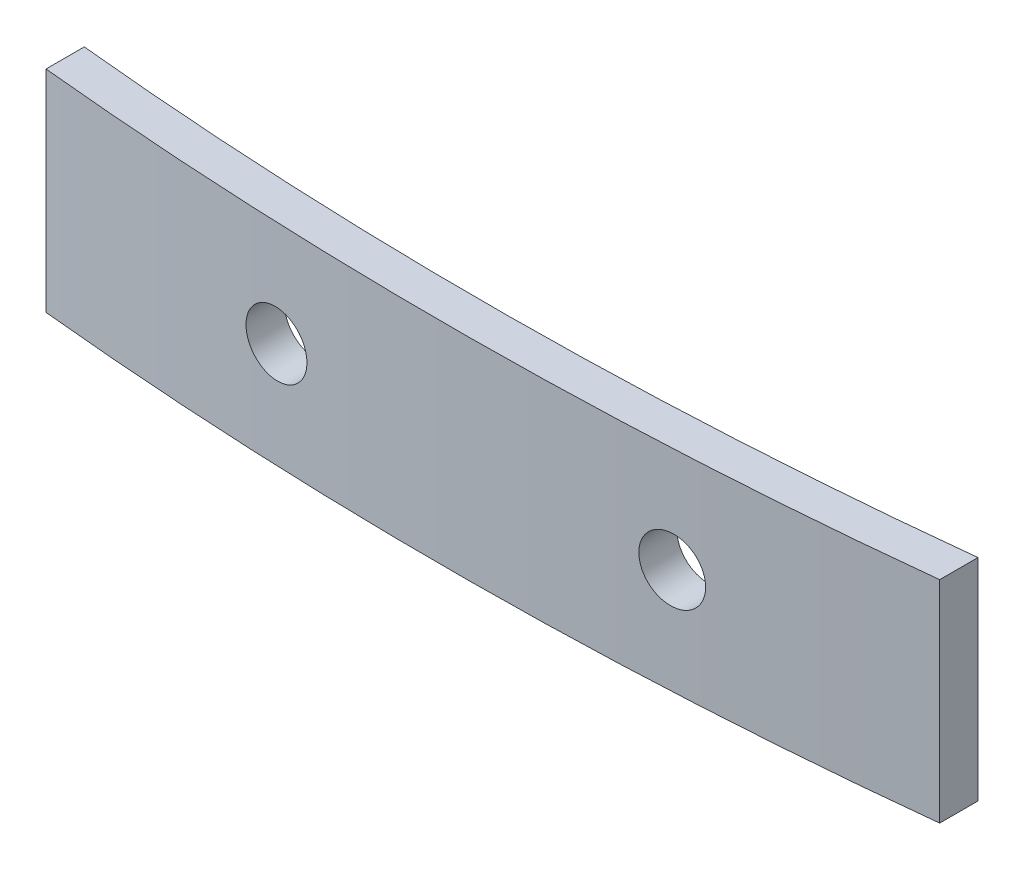
SolidWorks part; units mm, degrees
ref_plane "Front Plane" through (0, 0, 0) normal (0, 0, 1) x (1, 0, 0)
ref_plane "Top Plane" through (0, 0, 0) normal (0, 1, 0) x (1, 0, 0)
ref_plane "Right Plane" through (0, 0, 0) normal (1, 0, 0) x (0, 0, -1)
sketch "Sketch1" plane through (0, 0, 0) normal (0, 1, 0) x (1, 0, 0)
  line L0 (-35, 4.1426) -> (35, 4.5206) construction
  line L4 (-17.5, 10.9426) -> (-17.5, -8.9719) construction
  line L7 (-22.5, 18.3807) -> (-22.5, -8.9719) construction
  line L8 (22.5, 18.3807) -> (22.5, -9.9995) construction
  line L9 (17.5, -9.9995) -> (17.5, 10.9426) construction
  line L11 (17.5, -1.6885) -> (17.5, -3.1975)
  line L12 (-17.5, -1.8705) -> (-17.5, -3.378)
  arc A5 (-17.5, -1.8705) -> (17.5, -1.6885) centre (-0.865, 164.5106) ccw
  arc A6 (-17.5, -3.378) -> (17.5, -3.1975) centre (-0.865, 164.5106) ccw
  arc A8 (-35.4132, 0.908) -> (35.4342, 1.2875) centre (-0.865, 164.5106) ccw construction
  arc A9 (-35.7232, -0.5597) -> (35.7598, -0.1767) centre (-0.865, 164.5106) ccw construction
  point P4 (-35, 4.1426)
  point P5 (-35, 2.8648)
  point P7 (38.108, 5.4708)
  point P8 (35, 4.5206)
  point P10 (-0.865, 164.5106)
  point P11 (35, 3.2398)
  point P18 (-31.892, 5.0928)
  dimension "D1" = 45
  dimension "D2" = 1.5
  dimension "D3" = 70
  dimension "D4" = 22.5
  dimension "D6" = 17.5
  dimension "D5" = 35
extrude "Boss-Extrude1" add sketch "Sketch1" along normal blind 8.3
sketch "Sketch2" plane through (0, 0, 0) normal (0, 0, 1) x (1, 0, 0)
  line L0 (0, 8.3) -> (0, 0) construction
  line L1 (17.5, 8.3) -> (-17.5, 8.3) construction
  line L2 (-9, 4.15) -> (-6.5, 4.15) construction
  line L5 (6.5, 4.15) -> (9, 4.15) construction
  circle A0 centre (-7.75, 4.15) radius 1.25
  circle A1 centre (7.75, 4.15) radius 1.25
  point P15 (0, 0)
  dimension "D2" = 2.5
  dimension "D3" = 2.5
  dimension "D1" = 15.5
  dimension "D4" = 7.75
extrude "Cut-Extrude1" cut sketch "Sketch2" against normal through all both and the other way through all
